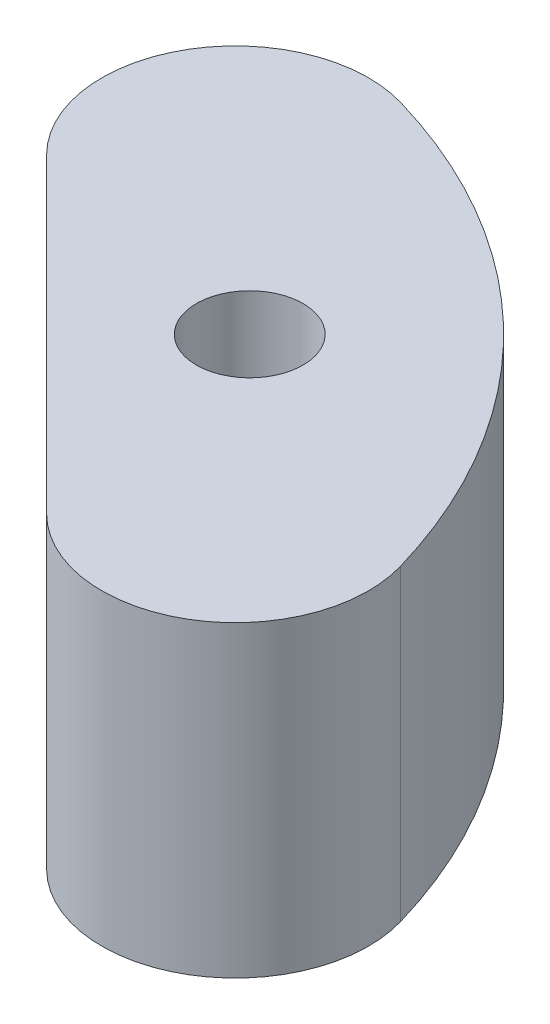
SolidWorks part; units mm, degrees
ref_plane "Front Plane" through (0, 0, 0) normal (0, 0, 1) x (1, 0, 0)
ref_plane "Top Plane" through (0, 0, 0) normal (0, 1, 0) x (1, 0, 0)
ref_plane "Right Plane" through (0, 0, 0) normal (1, 0, 0) x (0, 0, -1)
sketch "Sketch2" plane through (0, 0, 0) normal (0, 1, 0) x (1, 0, 0)
  line L1 (-17.9605, -17.9605) -> (17.9605, -17.9605) construction
  line L2 (-17.9605, -17.9605) -> (-17.9605, 17.9605) construction
  line L3 (-17.9605, 17.9605) -> (17.9605, 17.9605) construction
  line L4 (17.9605, -17.9605) -> (17.9605, 17.9605) construction
  line L5 (-17.9605, -17.9605) -> (17.9605, 17.9605) construction
  line L6 (-17.9605, 17.9605) -> (17.9605, -17.9605) construction
  line L7 (-11.3537, 34.7024) -> (34.7024, -11.3537)
  arc A1 (34.7024, -11.3537) -> (-11.3537, 34.7024) centre (0, 0) ccw
  circle A3 centre (17.9605, 17.9605) radius 3.302
  arc A4 (-11.3537, 34.7024) -> (34.7024, -11.3537) centre (0, 0) ccw construction
  dimension "D1" = 73.025
  dimension "D4" = 6.604
  dimension "D2" = 50.8
  dimension "D3" = 8.89
extrude "Boss-Extrude2" add sketch "Sketch2" along normal mid plane 19.05
sketch "Sketch4" plane through (11.6743, 0, -11.6743) normal (-0.7071, 0, 0.7071) x (0.7071, 0, 0.7071)
  line L1 (-9.97, 6.25) -> (9.97, 6.25) construction
  line L2 (-9.97, 6.25) -> (-9.97, -6.25) construction
  line L3 (-9.97, -6.25) -> (9.97, -6.25) construction
  line L4 (9.97, 6.25) -> (9.97, -6.25) construction
  line L5 (-9.97, 6.25) -> (9.97, -6.25) construction
  line L6 (-9.97, -6.25) -> (9.97, 6.25) construction
  circle A0 centre (9.97, 6.25) radius 1.95
  circle A1 centre (-9.97, 6.25) radius 1.95
  circle A2 centre (-9.97, -6.25) radius 1.95
  circle A3 centre (9.97, -6.25) radius 1.95
  point P0 (0, 0)
  dimension "D1" = 3.9
  dimension "D2" = 19.94
  dimension "D3" = 12.5
extrude "Cut-Extrude2" cut sketch "Sketch4" against normal blind 5.8
fillet "Fillet1" radius 8.255 2 edges at (-11.3537, 0, -34.7024) (34.7024, 0, 11.3537)
equation "\"AIRFRAME_OD\"= 3.142in"
equation "\"AIRFRAME_ID\"= 3.00in"
equation "\"FLAT_T\"= 0.125in"
equation "\"NOSE_EXP_L\"= 3.5in"
equation "\"NOSE_SHOULDER_L\"= 1.5in"
equation "\"MAIN_L\"= 30in"
equation "\"RECO_COUP_L\"= 6in"
equation "\"RECO_SWITCH_L\"= 1.5in"
equation "\"DROGUE_L\"= 14in"
equation "\"ATS_FORE_COUP_L\"= 4in"
equation "\"ATS_AFT_COUP_L\"= 2.5in"
equation "\"LOWER_L\"= 16in"
equation "\"FIN_N\"= 4"
equation "\"CR_AFT_X\"= 0.5in"
equation "\"CR_FORE_X\"= 6in"
equation "\"COUPLER_OD\"= 2.998in"
equation "\"COUPLER_ID\"= 2.875in"
equation "\"RECO_ROD_X\"= 1.5in"
equation "\"ATS_ROD_X\"= 2in"
equation "\"FIN_ROOT\"= 5in"
equation "\"FIN_X\"= 0.75in"
equation "\"MOTOR_OD\"= 2.25in"
equation "\"MOTOR_ID\"= 2.126in"
equation "\"MOTOR_L\"= 8in"
equation "\"MOTOR_LOWER_X\"= 0.5in"
equation "\"NOSE_CONE_L\"=14.5in"
equation "\"ATS_LIPO_L\" = 1.92in"
equation "\"ATS_LIPO_W\" = 0.42in"
equation "\"ATS_LIPO_H\" = 0.94in "
equation "\"ATS_STANDOFF_H\" = 10mm"
equation "\"ATS_STANDOFF_OD\" = 5.2mm"
equation "\"ATS_PCB_L\" = 2.5in"
equation "\"ATS_PCB_W\" = 1.45in"
equation "\"ATS_PCB_H\" = 1.2in"
equation "\"ATS_PCB_HOLESEP_W\" = 1.33in - 0.0985in"
equation "\"ATS_ALTI_L\" = 1.05in"
equation "\"ATS_ALTI_W\" = 0.7in"
equation "\"ATS_ALTI_H\" = 0.4in"
equation "\"D1@Sketch2\"=\"COUPLER_ID\""
